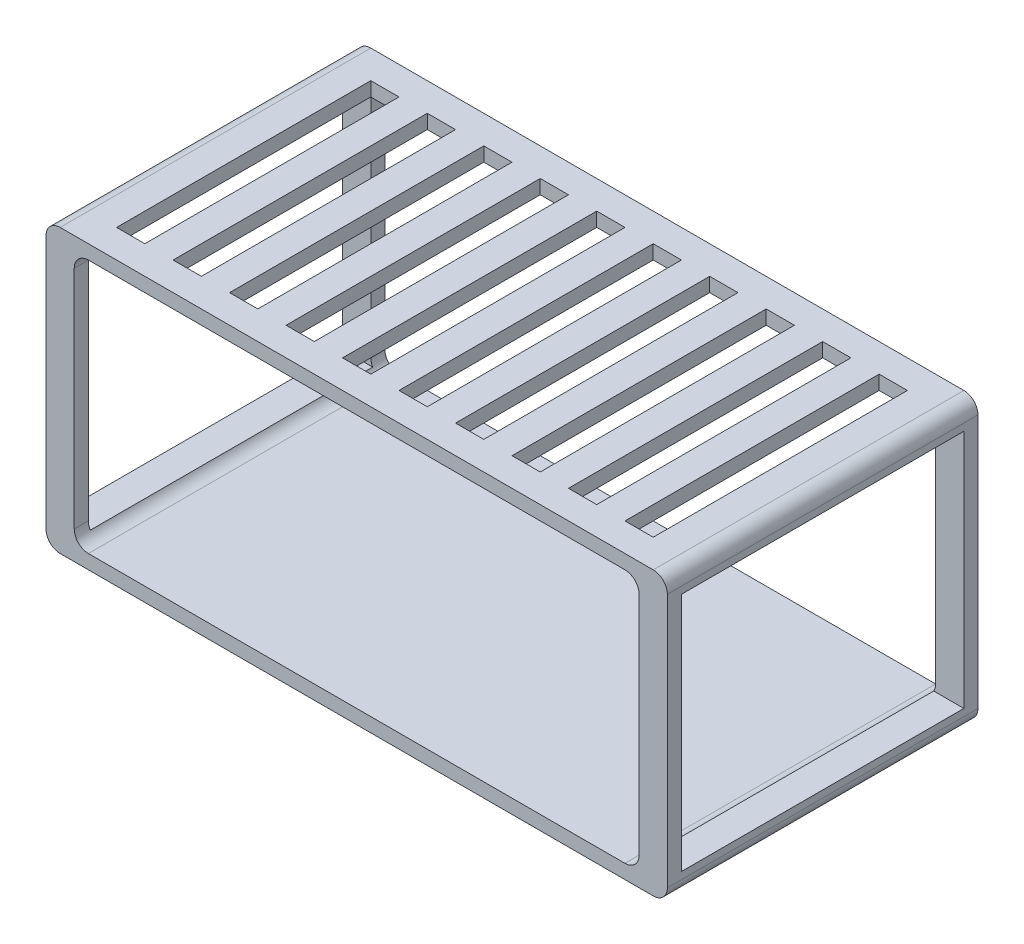
SolidWorks part; units mm, degrees
ref_plane "Front Plane" through (0, 0, 0) normal (0, 0, 1) x (1, 0, 0)
ref_plane "Top Plane" through (0, 0, 0) normal (0, 1, 0) x (1, 0, 0)
ref_plane "Right Plane" through (0, 0, 0) normal (1, 0, 0) x (0, 0, -1)
sketch "Sketch1" plane through (0, 0, 0) normal (0, 0, 1) x (1, 0, 0)
  line L1 (0, 0) -> (-2200, 0)
  line L2 (0, 0) -> (0, 1000)
  line L3 (0, 1000) -> (-2200, 1000)
  line L4 (-2200, 0) -> (-2200, 1000)
  dimension "D1" = 2200
  dimension "D2" = 1000
extrude "Boss-Extrude1" add sketch "Sketch1" along normal blind 1100
sketch "Sketch2" plane through (0, 0, 1100) normal (0, 0, 1) x (1, 0, 0)
  line L0 (-2200, 0) -> (0, 0) construction
  line L1 (-2100, 950) -> (-100, 950)
  line L2 (-2100, 950) -> (-2100, 50)
  line L3 (-2100, 50) -> (-100, 50)
  line L4 (-100, 950) -> (-100, 50)
  line L5 (0, 0) -> (0, 1000) construction
  dimension "D1" = 900
  dimension "D2" = 50
  dimension "D3" = 2000
  dimension "D4" = 100
extrude "Cut-Extrude1" cut sketch "Sketch2" against normal through all both and the other way through all
fillet "Fillet1" radius 50 8 edges at (-100, 50, 550) (-2100, 50, 550) (-100, 950, 550) (-2100, 950, 550) (-2200, 0, 550) (-2200, 1000, 550) (0, 0, 550) (0, 1000, 550)
sketch "Sketch3" plane through (0, 1000, 0) normal (0, 1, 0) x (1, 0, 0)
  line L1 (-2050, -100) -> (-1950, -100)
  line L2 (-2050, -100) -> (-2050, -1000)
  line L3 (-2050, -1000) -> (-1950, -1000)
  line L4 (-1950, -100) -> (-1950, -1000)
  line L6 (-2150, 0) -> (-2150, -1100) construction
  line L23 (-50, 0) -> (-2150, 0) construction
  line L58 (-1850, -100) -> (-1850, -1000)
  line L59 (-1750, -100) -> (-1750, -1000)
  line L60 (-1850, -100) -> (-1750, -100)
  line L61 (-1850, -1000) -> (-1750, -1000)
  line L62 (-1650, -100) -> (-1650, -1000)
  line L63 (-1550, -100) -> (-1550, -1000)
  line L64 (-1650, -100) -> (-1550, -100)
  line L65 (-1650, -1000) -> (-1550, -1000)
  line L66 (-1450, -100) -> (-1450, -1000)
  line L67 (-1350, -100) -> (-1350, -1000)
  line L68 (-1450, -100) -> (-1350, -100)
  line L69 (-1450, -1000) -> (-1350, -1000)
  line L70 (-1250, -100) -> (-1250, -1000)
  line L71 (-1150, -100) -> (-1150, -1000)
  line L72 (-1250, -100) -> (-1150, -100)
  line L73 (-1250, -1000) -> (-1150, -1000)
  line L74 (-1050, -100) -> (-1050, -1000)
  line L75 (-950, -100) -> (-950, -1000)
  line L76 (-1050, -100) -> (-950, -100)
  line L77 (-1050, -1000) -> (-950, -1000)
  line L78 (-850, -100) -> (-850, -1000)
  line L79 (-750, -100) -> (-750, -1000)
  line L80 (-850, -100) -> (-750, -100)
  line L81 (-850, -1000) -> (-750, -1000)
  line L82 (-650, -100) -> (-650, -1000)
  line L83 (-550, -100) -> (-550, -1000)
  line L84 (-650, -100) -> (-550, -100)
  line L85 (-650, -1000) -> (-550, -1000)
  line L86 (-450, -100) -> (-450, -1000)
  line L87 (-350, -100) -> (-350, -1000)
  line L88 (-450, -100) -> (-350, -100)
  line L89 (-450, -1000) -> (-350, -1000)
  line L90 (-250, -100) -> (-250, -1000)
  line L91 (-150, -100) -> (-150, -1000)
  line L92 (-250, -100) -> (-150, -100)
  line L93 (-250, -1000) -> (-150, -1000)
  dimension "D1" = 100
  dimension "D2" = 100
  dimension "D4" = 900
  dimension "D5" = 100
  dimension "D3" = 10
extrude "Cut-Extrude2" cut sketch "Sketch3" against normal up to next
sketch "Sketch4" plane through (0, 0, 0) normal (1, 0, 0) x (0, 0, -1)
  line L5 (-550, 950) -> (-550, 50) construction
  line L6 (-550, 50) -> (-550, 500) construction
  line L8 (-1050, 75) -> (-50, 75)
  line L9 (-1050, 75) -> (-1050, 925)
  line L10 (-1050, 925) -> (-50, 925)
  line L11 (-50, 75) -> (-50, 925)
  line L12 (-1050, 75) -> (-50, 925) construction
  line L13 (-1050, 925) -> (-50, 75) construction
  dimension "D1" = 1000
  dimension "D2" = 850
extrude "Cut-Extrude3" cut sketch "Sketch4" against normal through all both and the other way through all
